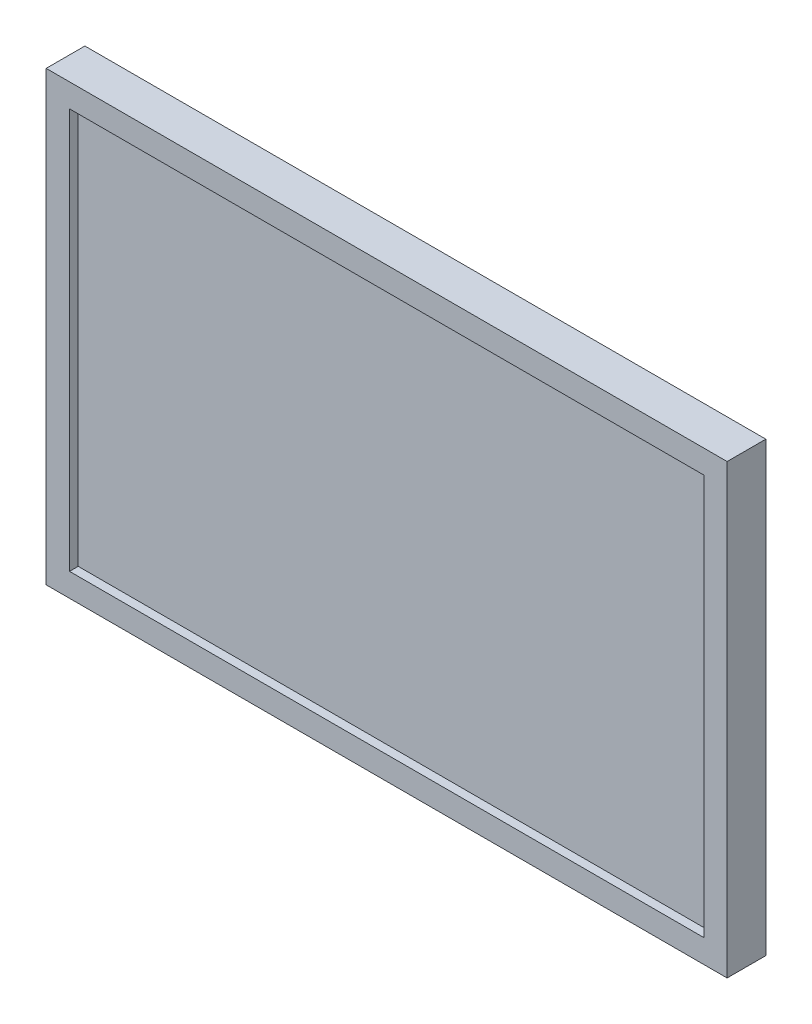
SolidWorks part; units mm, degrees
ref_plane "Front Plane" through (0, 0, 0) normal (0, 0, 1) x (1, 0, 0)
ref_plane "Top Plane" through (0, 0, 0) normal (0, 1, 0) x (1, 0, 0)
ref_plane "Right Plane" through (0, 0, 0) normal (1, 0, 0) x (0, 0, -1)
sketch "Sketch1" plane through (0, 0, 0) normal (0, 0, 1) x (1, 0, 0)
  line L1 (-255, -167.5) -> (255, -167.5)
  line L2 (-255, -167.5) -> (-255, 167.5)
  line L3 (-255, 167.5) -> (255, 167.5)
  line L4 (255, -167.5) -> (255, 167.5)
  line L5 (-255, -167.5) -> (255, 167.5) construction
  line L6 (-255, 167.5) -> (255, -167.5) construction
  point P0 (0, 0)
  dimension "D1" = 510
  dimension "D2" = 335
extrude "Boss-Extrude1" add sketch "Sketch1" against normal blind 29
sketch "Sketch2" plane through (0, 0, 0) normal (0, 0, 1) x (1, 0, 0)
  line L1 (237.5, -150) -> (-237.5, -150)
  line L2 (237.5, -150) -> (237.5, 150)
  line L3 (237.5, 150) -> (-237.5, 150)
  line L4 (-237.5, -150) -> (-237.5, 150)
  line L5 (237.5, -150) -> (-237.5, 150) construction
  line L6 (237.5, 150) -> (-237.5, -150) construction
  point P0 (0, 0)
  dimension "D1" = 475
  dimension "D2" = 300
extrude "Cut-Extrude1" cut sketch "Sketch2" against normal blind 6.5
sketch "Sketch3" plane through (0, 0, -29) normal (0, 0, -1) x (-1, 0, 0)
  line L0 (-255, 167.5) -> (255, 167.5) construction
  line L1 (-61, -60.5) -> (61, -60.5)
  line L2 (-61, -60.5) -> (-61, 61.5)
  line L3 (-61, 61.5) -> (61, 61.5)
  line L4 (61, -60.5) -> (61, 61.5)
  line L5 (-61, -60.5) -> (61, 61.5) construction
  line L6 (-61, 61.5) -> (61, -60.5) construction
  line L7 (0, 0.5) -> (0, 0) construction
  point P0 (0, 0.5)
  dimension "D1" = 106
  dimension "D2" = 122
  dimension "D3" = 122
extrude "Boss-Extrude2" add sketch "Sketch3" along normal blind 56
sketch "Sketch4" plane through (0, 0, -85) normal (0, 0, -1) x (-1, 0, 0)
  line L1 (-50, -50) -> (50, -50) construction
  line L2 (-50, -50) -> (-50, 50) construction
  line L3 (-50, 50) -> (50, 50) construction
  line L4 (50, -50) -> (50, 50) construction
  line L5 (-50, -50) -> (50, 50) construction
  line L6 (-50, 50) -> (50, -50) construction
  circle A0 centre (-50, 50) radius 2
  circle A1 centre (50, 50) radius 2
  circle A2 centre (50, -50) radius 2
  circle A3 centre (-50, -50) radius 2
  point P0 (0, 0)
  dimension "D1" = 4
  dimension "D2" = 100
  dimension "D3" = 100
extrude "Cut-Extrude2" cut sketch "Sketch4" against normal blind 10
sketch "Sketch5" plane through (0, 0, -85) normal (0, 0, -1) x (-1, 0, 0)
  line L1 (-125, -73.5) -> (125, -73.5)
  line L2 (-125, -73.5) -> (-125, 80.5)
  line L3 (-125, 80.5) -> (125, 80.5)
  line L4 (125, -73.5) -> (125, 80.5)
  line L5 (-125, -73.5) -> (125, 80.5) construction
  line L6 (-125, 80.5) -> (125, -73.5) construction
  line L10 (-61, -60.5) -> (61, -60.5)
  line L11 (61, -60.5) -> (61, 61.5)
  line L12 (61, 61.5) -> (-61, 61.5)
  line L13 (-61, 61.5) -> (-61, -60.5)
  line L14 (-61, -60.5) -> (61, -60.5)
  line L15 (61, -60.5) -> (61, 61.5)
  line L16 (61, 61.5) -> (-61, 61.5)
  line L17 (-61, 61.5) -> (-61, -60.5)
  point P0 (0, 3.5)
  point P5 (0, 0)
  point P8 (0, 0)
  dimension "D2" = 19
  dimension "D3" = 13
  dimension "D4" = 250
  dimension "D1" = 0
extrude "Boss-Extrude3" add sketch "Sketch5" along normal blind 7 and the other way up to surface
ref_plane "Plane1" through (0, -65.3296, -97.4759) normal (0, 0.5567, 0.8307) x (1, 0, 0)
sketch "Sketch7" plane through (0, -65.3296, -97.4759) normal (0, 0.5567, 0.8307) x (1, 0, 0)
  line L0 (255, -122.9949) -> (125, -9.8357)
  line L1 (-255, -122.9949) -> (255, -122.9949) construction
  line L2 (125, -9.8357) -> (-125, -9.8357) construction
  line L3 (-255, -122.9949) -> (255, -122.9949)
  line L4 (125, -9.8357) -> (-125, -9.8357)
  line L5 (-255, -122.9949) -> (-125, -9.8357)
extrude "Boss-Extrude4" add sketch "Sketch7" along normal up to body separate body
ref_plane "Plane2" through (-59.8785, 0, -123.5589) normal (0.4361, 0, 0.8999) x (0.8999, 0, -0.4361)
sketch "Sketch8" plane through (-59.8785, 0, -123.5589) normal (0.4361, 0, 0.8999) x (0.8999, 0, -0.4361)
  line L0 (-216.8266, 167.5) -> (-216.8266, -167.5) construction
  line L1 (-72.3655, -73.5) -> (-216.8266, -167.5) construction
  line L2 (-72.3655, -73.5) -> (-72.3655, 80.5) construction
  line L3 (-216.8266, 167.5) -> (-216.8266, -167.5)
  line L4 (-72.3655, -73.5) -> (-216.8266, -167.5)
  line L5 (-72.3655, -73.5) -> (-72.3655, 80.5)
  line L6 (-216.8266, 167.5) -> (-72.3655, 80.5)
extrude "Boss-Extrude5" add sketch "Sketch8" along normal up to body
sketch "Sketch9" plane through (0, 0, -92) normal (0, 0, -1) x (-1, 0, 0)
  line L0 (-255, 167.5) -> (255, 167.5) construction
  line L1 (125, 80.5) -> (-125, 80.5) construction
  line L2 (125, 80.5) -> (255, 167.5) construction
  line L3 (0, 167.5) -> (255, 167.5)
  line L4 (125, 80.5) -> (0, 80.5)
  line L5 (125, 80.5) -> (255, 167.5)
  line L6 (0, 80.5) -> (0, 167.5)
  point P6 (0, 80.5)
extrude "Cut-Extrude3" cut sketch "Sketch9" against normal up to surface (63 mm away) separate body up to face at (68.4218, 49.5372, -29)
mirror "Mirror1" about plane through (0, 0, 0) normal (1, 0, 0) of "Cut-Extrude3", "Boss-Extrude5"
